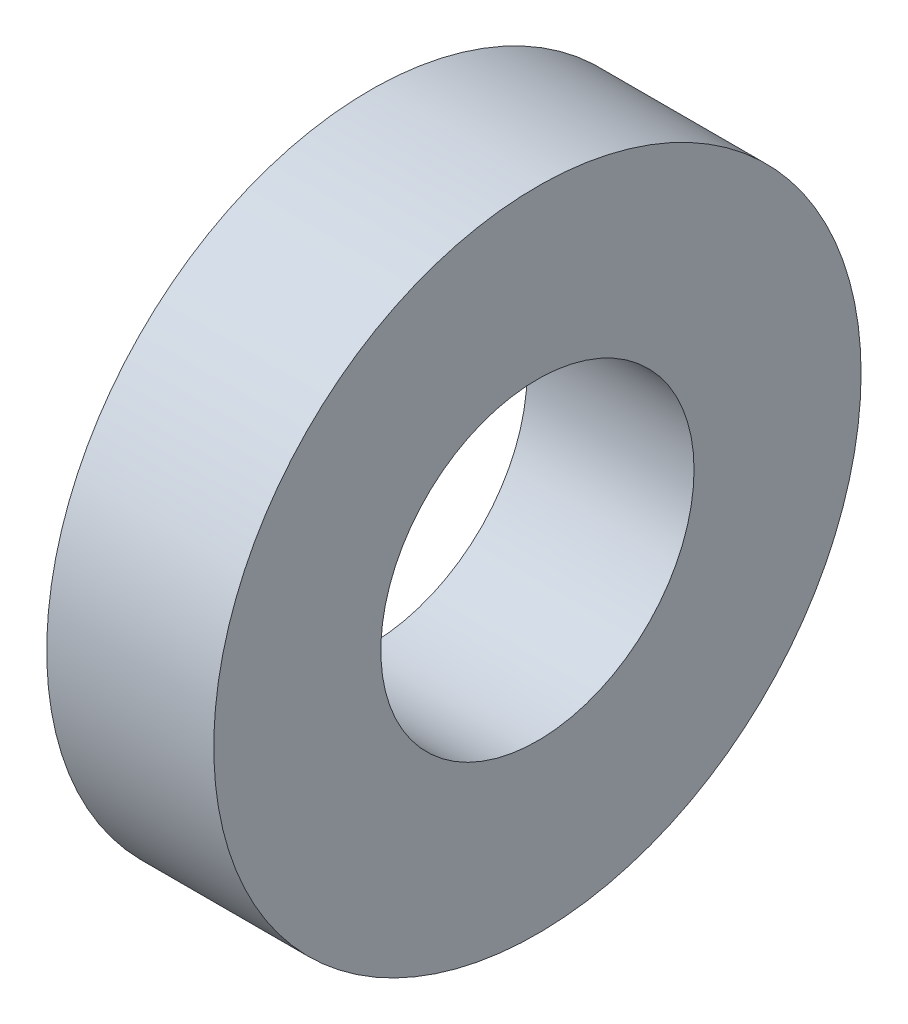
SolidWorks part; units mm, degrees
ref_plane "Front Plane" through (0, 0, 0) normal (0, 0, 1) x (1, 0, 0)
ref_plane "Top Plane" through (0, 0, 0) normal (0, 1, 0) x (1, 0, 0)
ref_plane "Right Plane" through (0, 0, 0) normal (1, 0, 0) x (0, 0, -1)
sketch "Sketch1" plane through (0, 0, 0) normal (1, 0, 0) x (0, 0, -1)
  circle A0 centre (0, 0) radius 31
  circle A1 centre (0, 0) radius 15
  dimension "D1" = 30
  dimension "D2" = 62
extrude "Boss-Extrude1" add sketch "Sketch1" along normal blind 16
